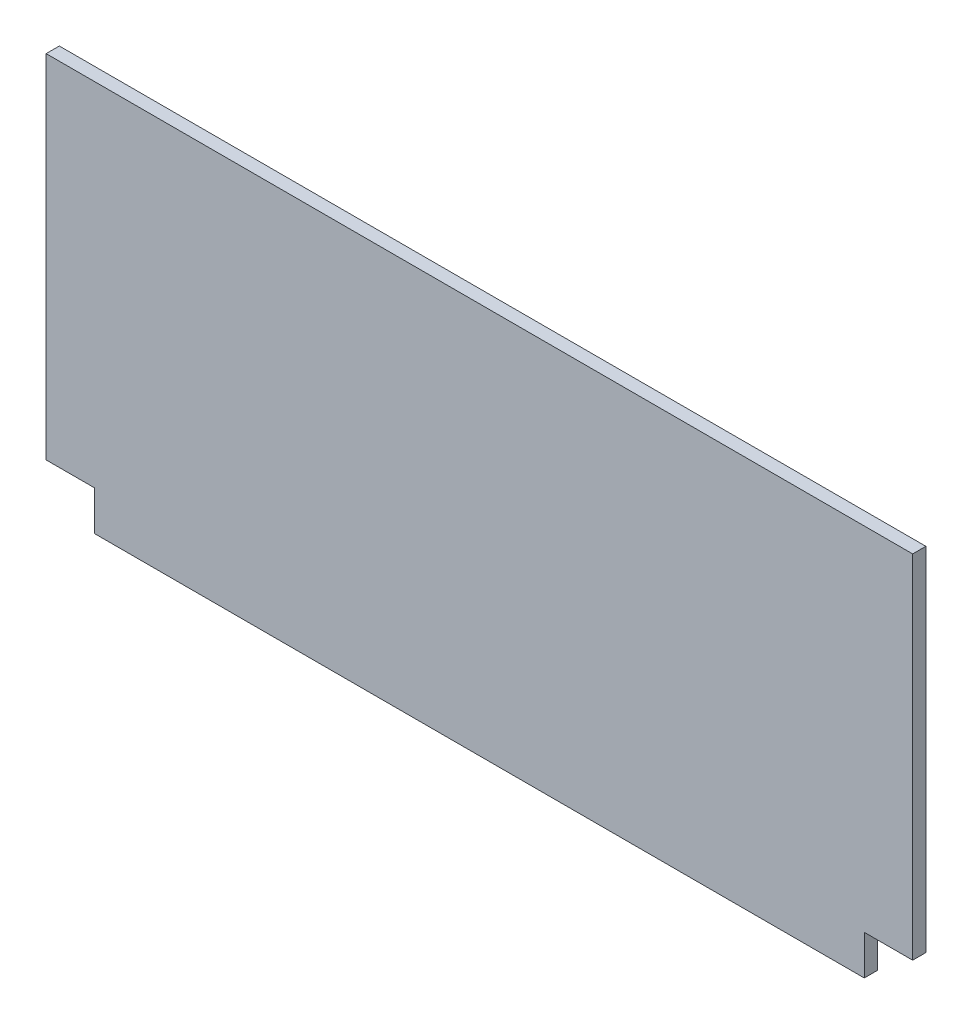
SolidWorks part; units mm, degrees
ref_plane "Ebene vorne" through (0, 0, 0) normal (0, 0, 1) x (1, 0, 0)
ref_plane "Ebene oben" through (0, 0, 0) normal (0, 1, 0) x (1, 0, 0)
ref_plane "Ebene rechts" through (0, 0, 0) normal (1, 0, 0) x (0, 0, -1)
sketch "Skizze1" plane through (0, 0, 0) normal (0, 0, 1) x (1, 0, 0)
  line L1 (-98.5, -44.5) -> (98.5, -44.5)
  line L2 (-98.5, -44.5) -> (-98.5, 44.5)
  line L3 (-98.5, 44.5) -> (98.5, 44.5)
  line L4 (98.5, -44.5) -> (98.5, 44.5)
  line L5 (-98.5, -44.5) -> (98.5, 44.5) construction
  line L6 (-98.5, 44.5) -> (98.5, -44.5) construction
  line L7 (-98.5, -44.5) -> (-87.5, -44.5)
  line L8 (-98.5, -44.5) -> (-98.5, -35.5)
  line L9 (-98.5, -35.5) -> (-87.5, -35.5)
  line L10 (-87.5, -44.5) -> (-87.5, -35.5)
  line L11 (98.5, -44.5) -> (87.5, -44.5)
  line L12 (98.5, -44.5) -> (98.5, -35.5)
  line L13 (98.5, -35.5) -> (87.5, -35.5)
  line L14 (87.5, -44.5) -> (87.5, -35.5)
  point P0 (0, 0)
  dimension "D1" = 197
  dimension "D2" = 89
  dimension "D3" = 11
  dimension "D4" = 11
  dimension "D5" = 9
  dimension "D6" = 9
extrude "Aufsatz-Linear austragen1" add sketch "Skizze1" along normal blind 3 contours L1 L14 L13 L4 L3 L2 L9 L10
